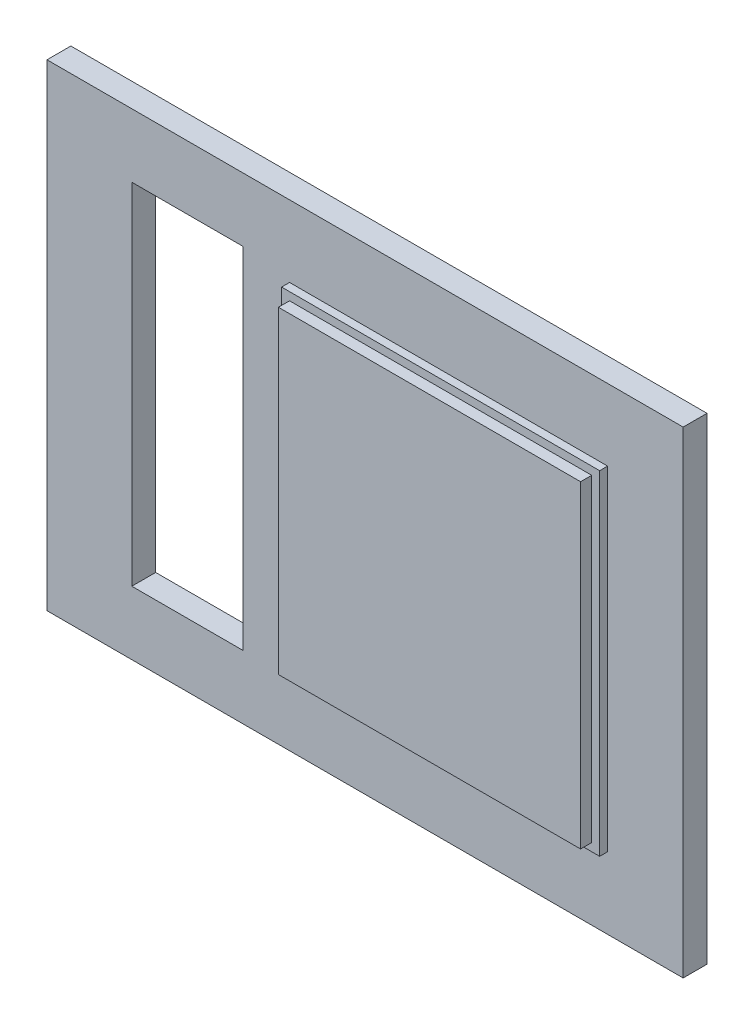
SolidWorks part; units mm, degrees
ref_plane "Front Plane" through (0, 0, 0) normal (0, 0, 1) x (1, 0, 0)
ref_plane "Top Plane" through (0, 0, 0) normal (0, 1, 0) x (1, 0, 0)
ref_plane "Right Plane" through (0, 0, 0) normal (1, 0, 0) x (0, 0, -1)
sketch "Sketch1" plane through (0, 0, 0) normal (0, 0, 1) x (1, 0, 0)
  line L1 (-20, 15) -> (20, 15)
  line L2 (-20, 15) -> (-20, -15)
  line L3 (-20, -15) -> (20, -15)
  line L4 (20, 15) -> (20, -15)
  line L5 (-20, 15) -> (20, -15) construction
  line L6 (-20, -15) -> (20, 15) construction
  point P0 (0, 0)
  dimension "D1" = 40
  dimension "D2" = 30
extrude "Boss-Extrude1" add sketch "Sketch1" along normal blind 1.5 contours L1 L4 L3 L2
sketch "Sketch2" plane through (0, 0, 1.5) normal (0, 0, 1) x (1, 0, 0)
  line L1 (-4.75, 10.5) -> (15.25, 10.5)
  line L2 (-4.75, 10.5) -> (-4.75, -10.5)
  line L3 (-4.75, -10.5) -> (15.25, -10.5)
  line L4 (15.25, 10.5) -> (15.25, -10.5)
  line L5 (-4.75, 10.5) -> (15.25, -10.5) construction
  line L6 (-4.75, -10.5) -> (15.25, 10.5) construction
  point P0 (5.25, 0)
  dimension "D1" = 21
  dimension "D2" = 20
extrude "Boss-Extrude2" add sketch "Sketch2" along normal blind 0.5
sketch "Sketch4" plane through (0, 0, 2) normal (0, 0, 1) x (1, 0, 0)
  line L1 (-4.25, 10) -> (14.75, 10)
  line L2 (-4.25, 10) -> (-4.25, -10)
  line L3 (-4.25, -10) -> (14.75, -10)
  line L4 (14.75, 10) -> (14.75, -10)
  line L5 (-4.25, 10) -> (14.75, -10) construction
  line L6 (-4.25, -10) -> (14.75, 10) construction
  point P0 (5.25, 0)
extrude "Boss-Extrude3" add sketch "Sketch4" along normal blind 0.7
sketch "Sketch5" plane through (0, 0, 1.5) normal (0, 0, 1) x (1, 0, 0)
  line L1 (-14.6667, 11) -> (-7.6667, 11)
  line L2 (-14.6667, 11) -> (-14.6667, -11)
  line L3 (-14.6667, -11) -> (-7.6667, -11)
  line L4 (-7.6667, 11) -> (-7.6667, -11)
  line L5 (-14.6667, 11) -> (-7.6667, -11) construction
  line L6 (-14.6667, -11) -> (-7.6667, 11) construction
  point P0 (-11.1667, 0)
extrude "Cut-Extrude1" cut sketch "Sketch5" against normal blind 1.5
